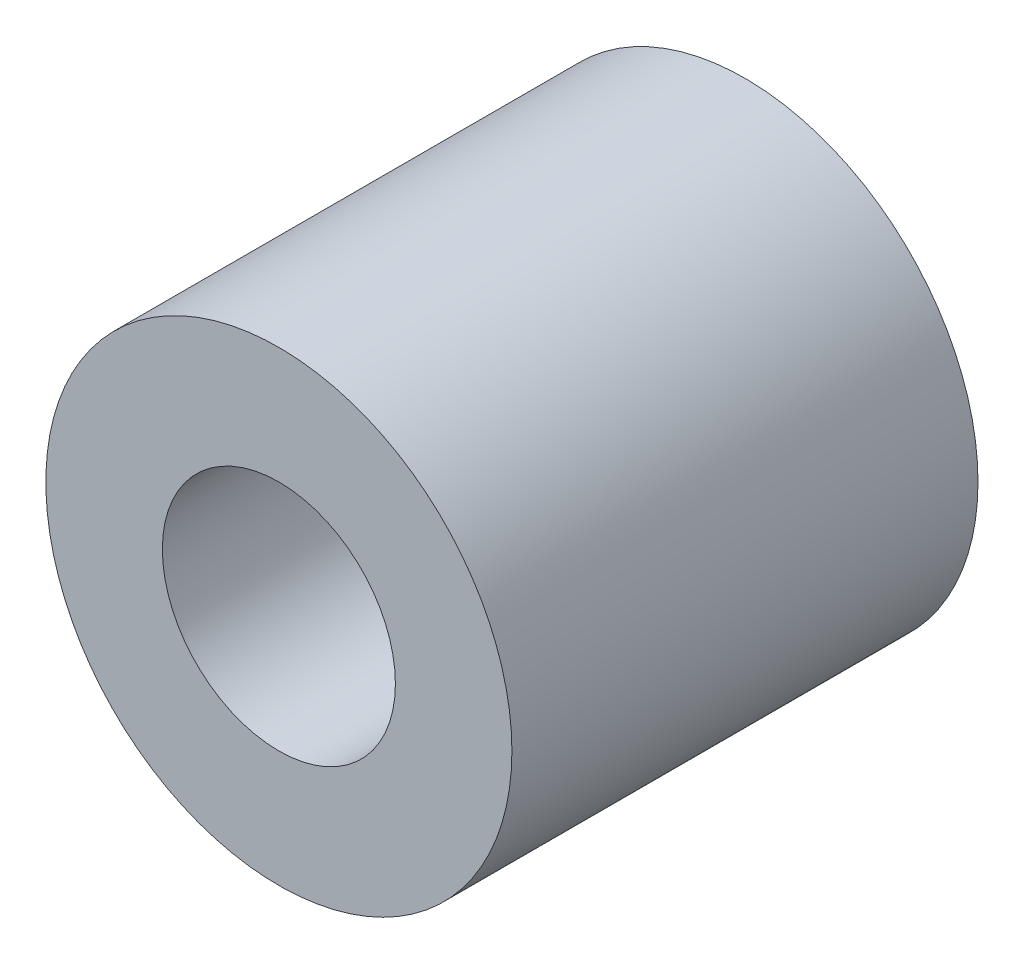
SolidWorks part; units mm, degrees
ref_plane "Płaszczyzna przednia" through (0, 0, 0) normal (0, 0, 1) x (1, 0, 0)
ref_plane "Płaszczyzna górna" through (0, 0, 0) normal (0, 1, 0) x (1, 0, 0)
ref_plane "Płaszczyzna prawa" through (0, 0, 0) normal (1, 0, 0) x (0, 0, -1)
sketch "Szkic1" plane through (0, 0, 0) normal (0, 0, 1) x (1, 0, 0)
  circle A0 centre (0, 0) radius 2.5
  dimension "D1" = 5
extrude "Dodanie-wyciągnięcie1" add sketch "Szkic1" along normal blind 5
hole_wizard "Otwór gwintowany M31" positions "Szkic 3D1" profile "Szkic2" tap size "M3" standard "ISO" end condition through all
sketch3d "Szkic 3D1"
  line L0 (0, 0, 5) -> (0, 0, 0) construction
  point P0 (0, 0, 5)
sketch "Szkic2" plane through (0, 0, 5) normal (1, 0, 0) x (0, -1, 0)
  line L0 (0, 0) -> (0, 5)
  line L1 (0, 5) -> (1.25, 5)
  line L2 (1.25, 5) -> (1.25, 0)
  line L5 (1.25, 0) -> (0, 0)
  line L11 (0, -6.35) -> (0, 107.95) construction
  dimension "Średnica otworu gwintowanego na wylot" = 2.5
  dimension "Głębokość otworu gwintowanego na wylot" = 5
cosmetic thread "Gwint otworu1"
